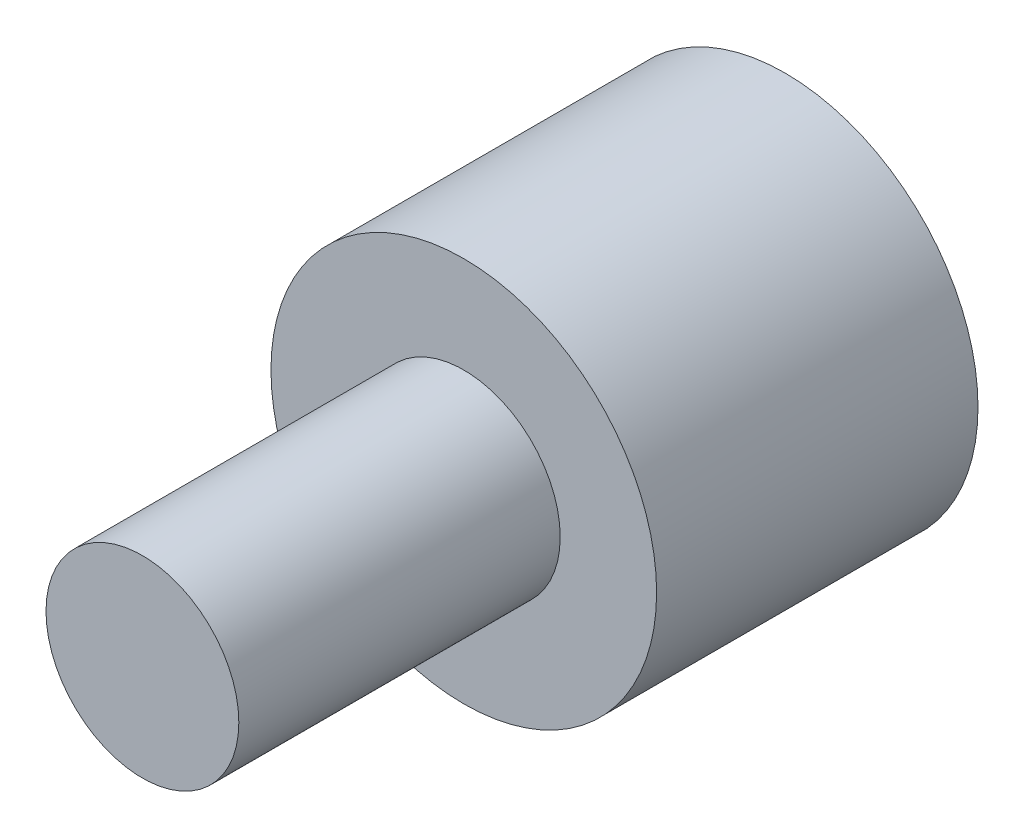
SolidWorks part; units mm, degrees
ref_plane "前基準面" through (0, 0, 0) normal (0, 0, 1) x (1, 0, 0)
ref_plane "上基準面" through (0, 0, 0) normal (0, 1, 0) x (1, 0, 0)
ref_plane "右基準面" through (0, 0, 0) normal (1, 0, 0) x (0, 0, -1)
sketch "草圖1" plane through (0, 0, 0) normal (0, 0, 1) x (1, 0, 0)
  circle A0 centre (0, 0) radius 12
  dimension "D1" = 24
extrude "填料-伸長2" add sketch "草圖1" along normal blind 20 contours A0
sketch "草圖2" plane through (0, 0, 20) normal (0, 0, 1) x (1, 0, 0)
  circle A0 centre (0, 0) radius 6
  dimension "D1" = 12
extrude "填料-伸長3" add sketch "草圖2" along normal blind 20 contours A0
sketch "草圖3" plane through (0, 0, 0) normal (0, 0, -1) x (-1, 0, 0)
  circle A0 centre (0, 0) radius 5
  dimension "D1" = 10
extrude "除料-伸長1" cut sketch "草圖3" against normal blind 12
